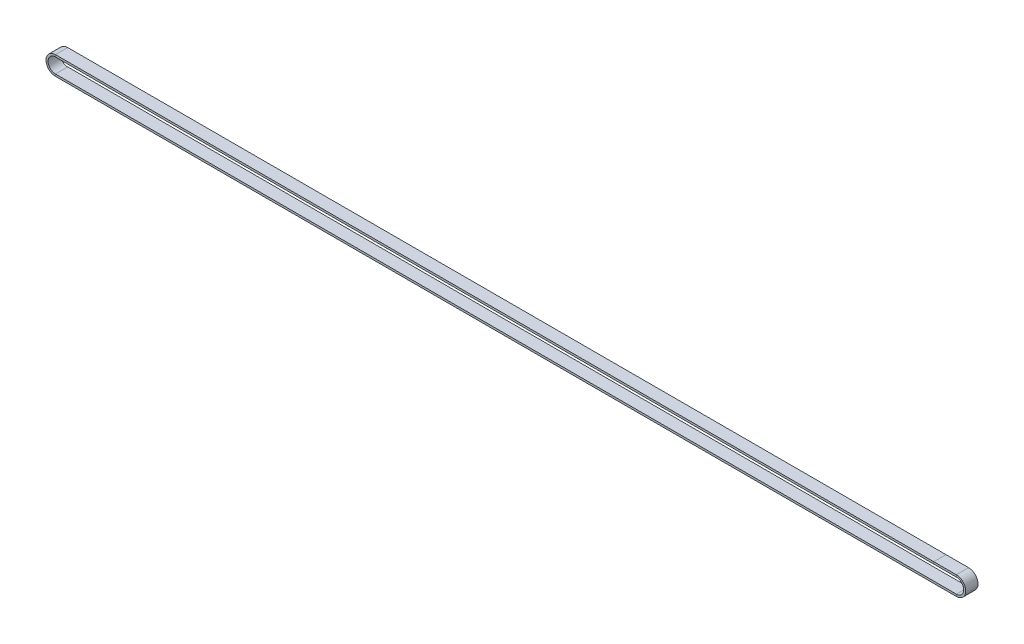
SolidWorks part; units mm, degrees
ref_plane "Front Plane" through (0, 0, 0) normal (0, 0, 1) x (1, 0, 0)
ref_plane "Top Plane" through (0, 0, 0) normal (0, 1, 0) x (1, 0, 0)
ref_plane "Right Plane" through (0, 0, 0) normal (1, 0, 0) x (0, 0, -1)
ref_plane "Plane1" through (-16, 0, 0) normal (1, 0, 0) x (0, 0, -1)
sketch "Sketch2" plane through (0, 0, 0) normal (0, 0, 1) x (1, 0, 0)
  line L0 (0, 0) -> (1, 0) construction
  line L1 (0, 0) -> (0, 1) construction
  line L2 (0.6, -6.9) -> (-660.3327, -6.9)
  line L3 (-660.3327, 6.9) -> (0.6, 6.9)
  arc A0 (0.6, 6.9) -> (0.6, -6.9) centre (0.6, 0) cw
  arc A1 (-660.3327, -6.9) -> (-660.3327, 6.9) centre (-660.3327, 0) cw
sketch "Sketch3" plane through (-16, 0, 0) normal (1, 0, 0) x (0, 0, -1)
  line L1 (0, 6.9) -> (-9, 6.9)
  line L2 (0, 6.9) -> (0, 5.4)
  line L3 (0, 5.4) -> (-9, 5.4)
  line L4 (-9, 6.9) -> (-9, 5.4)
  dimension "D1" = 1.5
  dimension "D2" = 9
sweep "Sweep1" add profiles "Sketch3" path "Sketch2"
move or copy body "Body-Move/Copy1" [suppressed] bodies to move or copy 101
